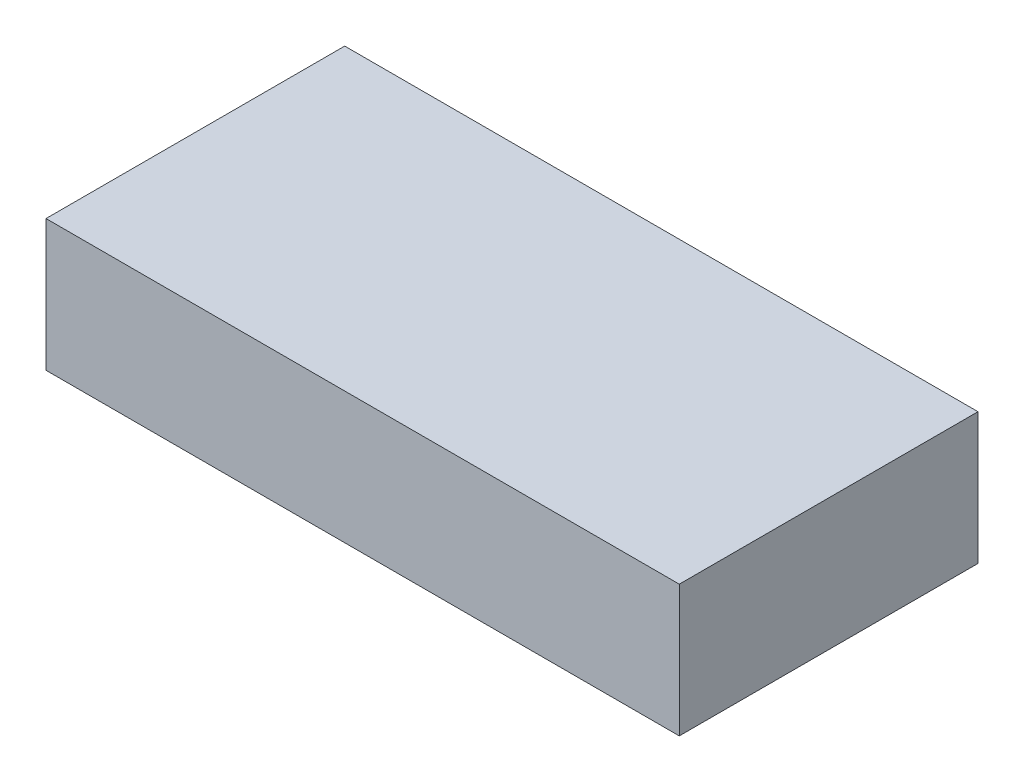
SolidWorks part; units mm, degrees
ref_plane "Front Plane" through (0, 0, 0) normal (0, 0, 1) x (1, 0, 0)
ref_plane "Top Plane" through (0, 0, 0) normal (0, 1, 0) x (1, 0, 0)
ref_plane "Right Plane" through (0, 0, 0) normal (1, 0, 0) x (0, 0, -1)
sketch "Sketch1" plane through (0, 0, 0) normal (0, 1, 0) x (1, 0, 0)
  line L1 (0, 0) -> (53, 0)
  line L2 (0, 0) -> (0, -25)
  line L3 (0, -25) -> (53, -25)
  line L4 (53, 0) -> (53, -25)
  dimension "D1" = 25
  dimension "D2" = 53
extrude "Boss-Extrude1" add sketch "Sketch1" along normal blind 11
